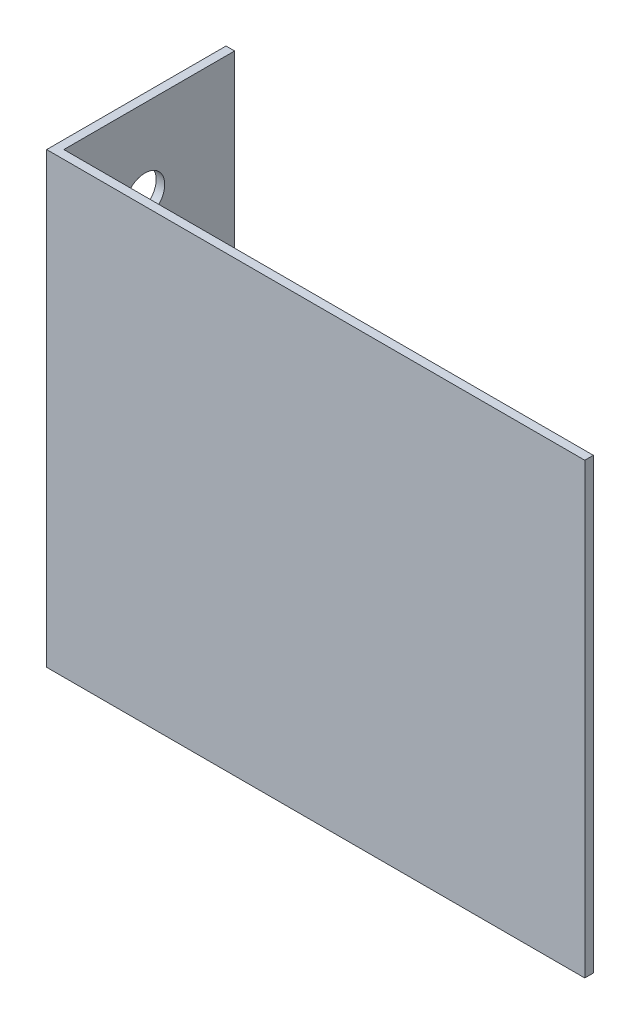
SolidWorks part; units mm, degrees
ref_plane "Front Plane" through (0, 0, 0) normal (0, 0, 1) x (1, 0, 0)
ref_plane "Top Plane" through (0, 0, 0) normal (0, 1, 0) x (1, 0, 0)
ref_plane "Right Plane" through (0, 0, 0) normal (1, 0, 0) x (0, 0, -1)
sketch "Sketch2" plane through (0, 0, 0) normal (0, 1, 0) x (1, 0, 0)
  line L0 (0, 0) -> (0, 25.4)
  line L1 (0, 25.4) -> (1.2141, 25.4)
  line L2 (1.2141, 25.4) -> (1.2141, 1.2141)
  line L3 (1.2141, 1.2141) -> (76.2, 1.2141)
  line L4 (76.2, 1.2141) -> (76.2, 0)
  line L5 (76.2, 0) -> (0, 0)
  dimension "D1" = 25.4
  dimension "D2" = 76.2
  dimension "D3" = 1.2141
  dimension "D4" = 1.2141
extrude "Boss-Extrude1" add sketch "Sketch2" along normal blind 63.5
sketch "Sketch3" plane through (0, 0, 0) normal (-1, 0, 0) x (0, 0, 1)
  line L1 (-25.4, 63.5) -> (0, 63.5) construction
  line L2 (-25.4, 0) -> (0, 0) construction
  line L3 (-12.7, 52.07) -> (-12.7, 63.5)
  line L4 (-12.7, 11.43) -> (-12.7, 0)
  circle A0 centre (-12.7, 52.07) radius 2.8067
  circle A1 centre (-12.7, 11.43) radius 2.8067
  dimension "D1" = 5.6134
  dimension "D2" = 40.64
extrude "Cut-Extrude1" cut sketch "Sketch3" against normal blind 2.54
